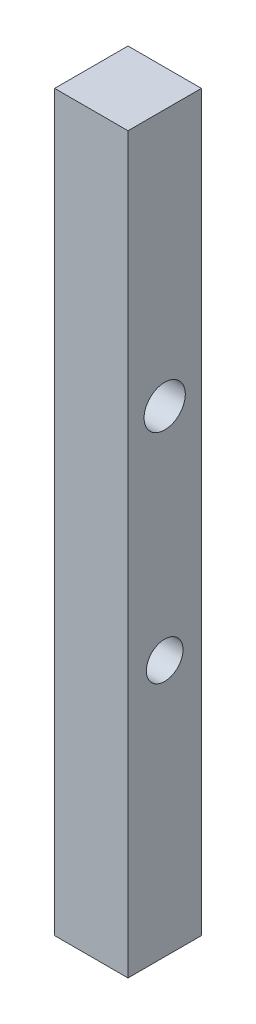
SolidWorks part; units mm, degrees
ref_plane "Front Plane" through (0, 0, 0) normal (0, 0, 1) x (1, 0, 0)
ref_plane "Top Plane" through (0, 0, 0) normal (0, 1, 0) x (1, 0, 0)
ref_plane "Right Plane" through (0, 0, 0) normal (1, 0, 0) x (0, 0, -1)
sketch "Sketch1" plane through (0, 0, 0) normal (0, 1, 0) x (1, 0, 0)
  line L1 (0, 0) -> (-25.4, 0)
  line L2 (0, 0) -> (0, 25.4)
  line L3 (0, 25.4) -> (-25.4, 25.4)
  line L4 (-25.4, 0) -> (-25.4, 25.4)
  dimension "D1" = 25.4
  dimension "D2" = 25.4
extrude "Boss-Extrude1" add sketch "Sketch1" along normal blind 254
sketch "Sketch2" plane through (0, 0, 0) normal (1, 0, 0) x (0, 0, -1)
  line L0 (0, 254) -> (0, 0) construction
  line L1 (0, 254) -> (25.4, 254) construction
  line L2 (0, 0) -> (25.4, 0) construction
  circle A0 centre (12.7, 165.1) radius 7.1393
  circle A1 centre (12.7, 88.9) radius 6.35
  point P8 (12.7, 254)
  point P11 (12.7, 0)
  dimension "D3" = 12.7
  dimension "D1" = 76.2
  dimension "D2" = 12.7
  dimension "D4" = 88.9
  dimension "D5" = 88.9
extrude "Cut-Extrude1" cut sketch "Sketch2" against normal through all
